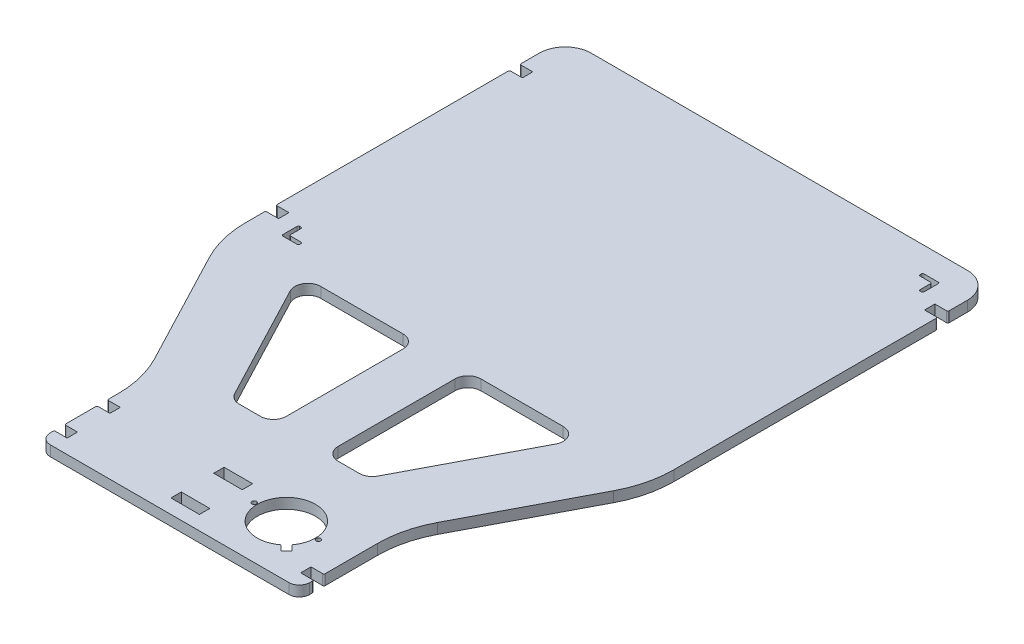
SolidWorks part; units mm, degrees
ref_plane "Front Plane" through (0, 0, 0) normal (0, 0, 1) x (1, 0, 0)
ref_plane "Top Plane" through (0, 0, 0) normal (0, 1, 0) x (1, 0, 0)
ref_plane "Right Plane" through (0, 0, 0) normal (1, 0, 0) x (0, 0, -1)
sketch "Sketch1" plane through (0, 0, 0) normal (0, 1, 0) x (1, 0, 0)
  line L0 (92, 0) -> (-92, 0)
  line L1 (-100, 8) -> (-100, 10)
  line L2 (-109.1447, 97.4452) -> (-155.8553, 186.5548)
  line L3 (-165, 223.6967) -> (-165, 238)
  line L4 (-145, 470) -> (145, 470)
  line L5 (0, 0) -> (0, 539.5591) construction
  line L6 (-164, 435) -> (-155, 435)
  line L7 (-155, 435) -> (-155, 427)
  line L8 (-155, 427) -> (-164, 427)
  line L9 (-165, 436) -> (-165, 450)
  line L10 (-164, 247) -> (-155, 247)
  line L11 (-139.7, 232) -> (139.7, 232) construction
  line L12 (-139.7, 232) -> (-139.7, 447.9) construction
  line L13 (-139.7, 447.9) -> (139.7, 447.9) construction
  line L14 (139.7, 232) -> (139.7, 447.9) construction
  line L15 (-139.7, 232) -> (139.7, 447.9) construction
  line L16 (-139.7, 447.9) -> (139.7, 232) construction
  line L17 (-155, 247) -> (-155, 239)
  line L18 (-155, 239) -> (-164, 239)
  line L19 (-165, 248) -> (-165, 426)
  line L20 (139.7, 447.9) -> (-139.7, 232) construction
  line L21 (139.7, 232) -> (-139.7, 447.9) construction
  line L22 (139.7, 232) -> (139.7, 447.9) construction
  line L23 (165, 247) -> (165, 426)
  line L24 (165, 247) -> (165, 239)
  line L25 (-139.7, 241) -> (-139.7, 233)
  line L26 (-138.7, 232) -> (-130.7, 232)
  line L27 (165, 436) -> (165, 450)
  line L28 (155, 427) -> (164, 427)
  line L29 (155, 435) -> (155, 427)
  line L30 (164, 435) -> (155, 435)
  line L31 (165, 223.6967) -> (165, 239)
  line L32 (109.1447, 97.4452) -> (155.8553, 186.5548)
  line L33 (100, 8) -> (100, 10)
  line L34 (-99, 52) -> (-90, 52)
  line L35 (-10, 52) -> (12, 52)
  line L36 (-10, 52) -> (-10, 44)
  line L37 (-10, 44) -> (12, 44)
  line L38 (12, 52) -> (12, 44)
  line L39 (-10, 52) -> (12, 44) construction
  line L40 (-10, 44) -> (12, 52) construction
  line L41 (-10, 19) -> (12, 19)
  line L42 (-10, 19) -> (-10, 11)
  line L43 (-10, 11) -> (12, 11)
  line L44 (12, 19) -> (12, 11)
  line L45 (-10, 19) -> (12, 11) construction
  line L46 (-10, 11) -> (12, 19) construction
  line L47 (-90, 52) -> (-90, 44)
  line L48 (-90, 44) -> (-99, 44)
  line L49 (-99, 19) -> (-90, 19)
  line L50 (-90, 19) -> (-90, 11)
  line L51 (-90, 11) -> (-99, 11)
  line L52 (99, 19) -> (90, 19)
  line L53 (90, 19) -> (90, 11)
  line L54 (90, 11) -> (99, 11)
  line L55 (-100, 53) -> (-100, 60.3033)
  line L56 (-100, 20) -> (-100, 43)
  line L57 (100, 20) -> (100, 60.3033)
  line L58 (-102.3244, 195.3573) -> (-55.147, 105.3573)
  line L59 (-46.29, 100) -> (-30, 100)
  line L60 (-20, 110) -> (-20, 200)
  line L61 (-30, 210) -> (-93.4675, 210)
  line L62 (30, 210) -> (93.4675, 210)
  line L63 (20, 110) -> (20, 200)
  line L64 (46.29, 100) -> (30, 100)
  line L65 (102.3244, 195.3573) -> (55.147, 105.3573)
  line L66 (-129.7, 231) -> (-129.7, 230)
  line L67 (-130.7, 229) -> (-141.7, 229)
  line L68 (-142.7, 230) -> (-142.7, 241)
  line L69 (-141.7, 242) -> (-140.7, 242)
  line L70 (129.7, 449.9) -> (129.7, 448.9)
  line L71 (130.7, 447.9) -> (138.7, 447.9)
  line L72 (139.7, 446.9) -> (139.7, 438.9)
  line L73 (140.7, 437.9) -> (141.7, 437.9)
  line L74 (142.7, 438.9) -> (142.7, 449.9)
  line L75 (141.7, 450.9) -> (130.7, 450.9)
  line L76 (50, 40) -> (76.015, 13.985) construction
  line L77 (67.8892, 26.3535) -> (72.1318, 22.1108)
  line L78 (72.1318, 22.1108) -> (67.8892, 17.8682)
  line L79 (67.8892, 17.8682) -> (63.6465, 22.1108)
  circle A0 centre (50, 40) radius 24.74 construction
  arc A1 (67.8892, 26.3535) -> (63.6465, 22.1108) centre (50, 40) ccw
  circle A2 centre (74.74, 40) radius 1.75
  circle A3 centre (25.26, 40) radius 1.75
  circle A4 centre (-50, 40) radius 24.74 construction
  circle A5 centre (-25.26, 40) radius 1.75
  circle A6 centre (-74.74, 40) radius 1.75
  circle A7 centre (-50, 40) radius 22.5
  arc A8 (-20, 110) -> (-30, 100) centre (-30, 110) cw
  arc A9 (-46.29, 100) -> (-55.147, 105.3573) centre (-46.29, 110) cw
  arc A10 (-102.3244, 195.3573) -> (-93.4675, 210) centre (-93.4675, 200) cw
  arc A11 (-30, 210) -> (-20, 200) centre (-30, 200) cw
  arc A12 (30, 210) -> (20, 200) centre (30, 200) ccw
  arc A13 (20, 110) -> (30, 100) centre (30, 110) ccw
  arc A14 (55.147, 105.3573) -> (46.29, 100) centre (46.29, 110) cw
  arc A15 (102.3244, 195.3573) -> (93.4675, 210) centre (93.4675, 200) ccw
  arc A16 (-165, 223.6967) -> (-155.8553, 186.5548) centre (-85, 223.6967) ccw
  arc A17 (-100, 60.3033) -> (-109.1447, 97.4452) centre (-180, 60.3033) ccw
  arc A18 (100, 60.3033) -> (109.1447, 97.4452) centre (180, 60.3033) cw
  arc A19 (155.8553, 186.5548) -> (165, 223.6967) centre (85, 223.6967) ccw
  arc A20 (-165, 450) -> (-145, 470) centre (-145, 450) cw
  arc A21 (165, 450) -> (145, 470) centre (145, 450) ccw
  arc A22 (-92, 0) -> (-100, 8) centre (-92, 8) cw
  arc A23 (92, 0) -> (100, 8) centre (92, 8) ccw
  arc A24 (-142.7, 230) -> (-141.7, 229) centre (-141.7, 230) ccw
  arc A25 (-130.7, 229) -> (-129.7, 230) centre (-130.7, 230) ccw
  arc A26 (-129.7, 231) -> (-130.7, 232) centre (-130.7, 231) ccw
  arc A27 (-138.7, 232) -> (-139.7, 233) centre (-138.7, 233) cw
  arc A28 (-139.7, 241) -> (-140.7, 242) centre (-140.7, 241) ccw
  arc A29 (-142.7, 241) -> (-141.7, 242) centre (-141.7, 241) cw
  arc A30 (140.7, 437.9) -> (139.7, 438.9) centre (140.7, 438.9) cw
  arc A31 (141.7, 437.9) -> (142.7, 438.9) centre (141.7, 438.9) ccw
  arc A32 (142.7, 449.9) -> (141.7, 450.9) centre (141.7, 449.9) ccw
  arc A33 (139.7, 446.9) -> (138.7, 447.9) centre (138.7, 446.9) ccw
  arc A34 (130.7, 447.9) -> (129.7, 448.9) centre (130.7, 448.9) cw
  arc A35 (129.7, 449.9) -> (130.7, 450.9) centre (130.7, 449.9) cw
  arc A36 (165, 436) -> (164, 435) centre (164, 436) cw
  arc A37 (165, 426) -> (164, 427) centre (164, 426) ccw
  arc A38 (-165, 436) -> (-164, 435) centre (-164, 436) ccw
  arc A39 (-165, 426) -> (-164, 427) centre (-164, 426) cw
  arc A40 (-165, 238) -> (-164, 239) centre (-164, 238) cw
  arc A41 (-165, 248) -> (-164, 247) centre (-164, 248) ccw
  arc A42 (-100, 53) -> (-99, 52) centre (-99, 53) ccw
  arc A43 (-99, 44) -> (-100, 43) centre (-99, 43) ccw
  arc A44 (-100, 10) -> (-99, 11) centre (-99, 10) cw
  arc A45 (-100, 20) -> (-99, 19) centre (-99, 20) ccw
  arc A46 (100, 10) -> (99, 11) centre (99, 10) ccw
  arc A47 (100, 20) -> (99, 19) centre (99, 20) cw
  point P3 (0, 339.95)
  point P31 (0, 470)
  point P34 (0, 0)
  point P78 (-20, 100)
  point P81 (-52.3387, 100)
  point P84 (-110, 210)
  point P87 (-20, 210)
  point P90 (20, 210)
  point P93 (20, 100)
  point P96 (52.3387, 100)
  point P99 (110, 210)
  point P102 (-165, 204)
  point P105 (-100, 80)
  point P108 (100, 80)
  point P111 (165, 204)
  point P114 (-165, 470)
  point P117 (165, 470)
  point P118 (-100, 0)
  point P121 (100, 0)
  point P133 (-129.7, 232)
  point P139 (-139.7, 242)
  point P142 (-142.7, 242)
  point P150 (139.7, 437.9)
  point P160 (129.7, 447.9)
  point P163 (129.7, 450.9)
  point P169 (70.0105, 19.9895)
  point P170 (70.0105, 19.9895)
  point P172 (165, 435)
  point P175 (165, 427)
  point P178 (-165, 435)
  point P181 (-165, 427)
  point P184 (-165, 239)
  point P187 (-165, 247)
  point P190 (-100, 52)
  point P193 (-100, 44)
  point P198 (-100, 19)
  point P203 (100, 19)
  dimension "D15" = 45
  dimension "D16" = 49.48
  dimension "D17" = 3.5
  dimension "D28" = 10
  dimension "D29" = 80
  dimension "D30" = 20
  dimension "D31" = 8
  dimension "D34" = 1
  dimension "D37" = 1
  dimension "D41" = 1
  dimension "D1" = 266
  dimension "D2" = 204
  dimension "D3" = 80
  dimension "D4" = 100
  dimension "D5" = 165
  dimension "D6" = 8
  dimension "D7" = 10
  dimension "D8" = 35
  dimension "D9" = 279.4
  dimension "D10" = 215.9
  dimension "D11" = 232
  dimension "D12" = 35
  dimension "D13" = 40
  dimension "D14" = 50
  dimension "D18" = 22
  dimension "D19" = 8
  dimension "D20" = 25
  dimension "D21" = 11
  dimension "D22" = 12
  dimension "D23" = 10
  dimension "D24" = 20
  dimension "D25" = 110
  dimension "D26" = 100
  dimension "D27" = 90
  dimension "D32" = 3
  dimension "D33" = 10
  dimension "D35" = 10
  dimension "D36" = 3
  dimension "D38" = 45
  dimension "D39" = 6
  dimension "D40" = 6
extrude "Boss-Extrude1" add sketch "Sketch1" along normal blind 8 contours L0 A23 L33 L54 L53 L52 L57 A18 L32 A19 L31 L24 L23 L28 L29 L30 L27 A21 L4 A20 L9 L6 L7 L8 L19 L10 L17 L18 L3 A16 L2 A17 L55 L34 L47 L48 L56 L49 L50 L51 L1 A22 L61 A11 L60 A8 L59 A9 L58 A10 | A7 A6 A5 | A5 A7 | A6 A7
